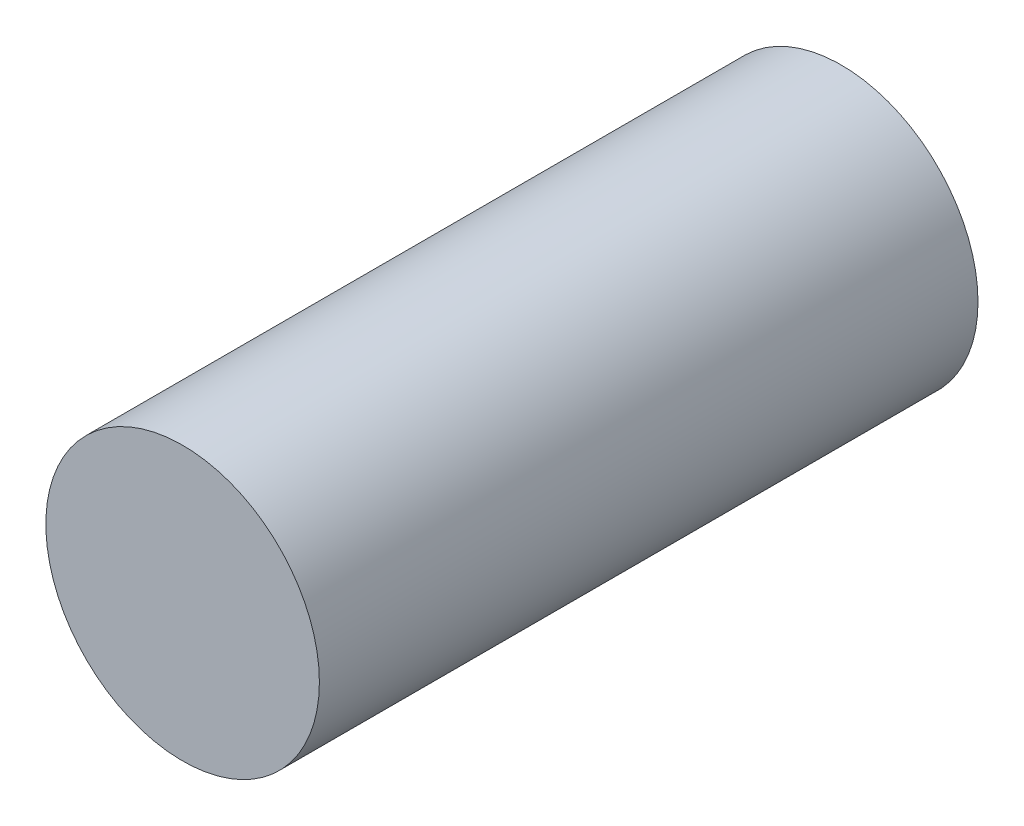
SolidWorks part; units mm, degrees
ref_plane "Plane1" through (0, 0, 0) normal (0, 0, 1) x (1, 0, 0)
ref_plane "Plane2" through (0, 0, 0) normal (0, 1, 0) x (1, 0, 0)
ref_plane "Plane3" through (0, 0, 0) normal (1, 0, 0) x (0, 0, -1)
sketch "Эскиз1" plane through (0, 0, 0) normal (0, 0, 1) x (1, 0, 0)
  circle A0 centre (689, 689) radius 623
extrude "Вытянуть1" add sketch "Эскиз1" against normal blind 3000
